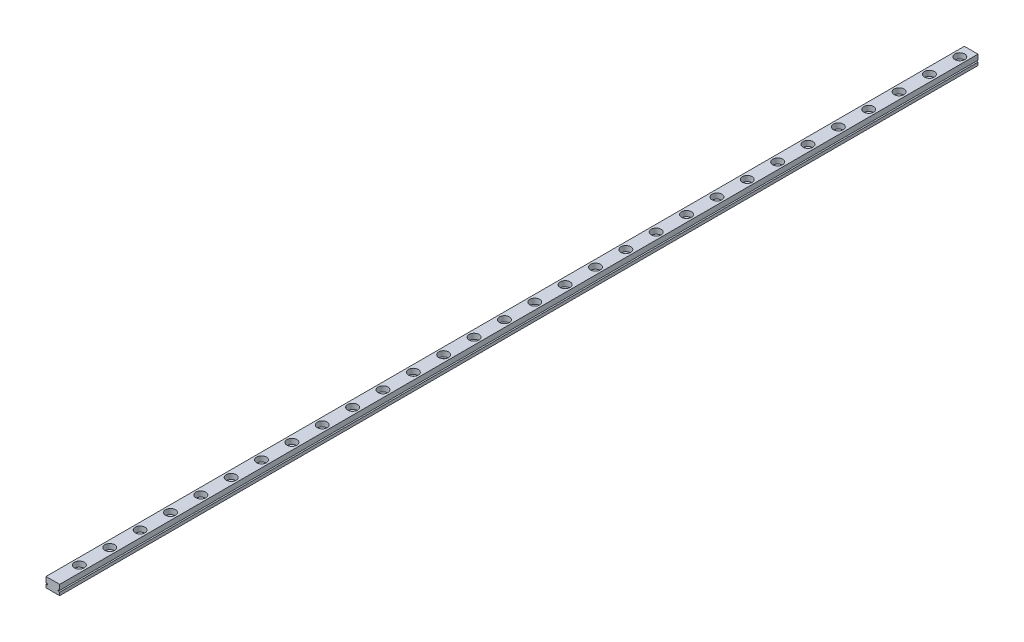
SolidWorks part; units mm, degrees
material "不锈钢 (铁素体)"
ref_plane "前视基准面" through (0, 0, 0) normal (0, 0, 1) x (1, 0, 0)
ref_plane "上视基准面" through (0, 0, 0) normal (0, 1, 0) x (1, 0, 0)
ref_plane "右视基准面" through (0, 0, 0) normal (1, 0, 0) x (0, 0, -1)
sketch "草图1" plane through (0, 0, 0) normal (0, 0, 1) x (1, 0, 0)
  line L1 (-4.5, 3.25) -> (4.5, 3.25)
  line L2 (-4.5, 3.25) -> (-4.5, -3.25)
  line L3 (-4.5, -3.25) -> (4.5, -3.25)
  line L4 (4.5, 3.25) -> (4.5, -3.25)
  line L5 (-4.5, 3.25) -> (4.5, -3.25) construction
  line L6 (-4.5, -3.25) -> (4.5, 3.25) construction
  point P0 (0, 0)
  dimension "D1" = 6.5
  dimension "D2" = 9
extrude "凸台-拉伸1" add sketch "草图1" along normal blind 608
sketch "草图2" plane through (0, 3.25, 0) normal (0, 1, 0) x (1, 0, 0)
  line L0 (0, 0) -> (0, -84.8716) construction
  line L1 (4.5, 0) -> (-4.5, 0) construction
  circle A0 centre (0, -7.5) radius 1.75
  circle A1 centre (0, -27.5) radius 1.75
  circle A2 centre (0, -47.5) radius 1.75
  circle A3 centre (0, -67.5) radius 1.75
  circle A4 centre (0, -87.5) radius 1.75
  circle A5 centre (0, -107.5) radius 1.75
  circle A6 centre (0, -127.5) radius 1.75
  circle A7 centre (0, -147.5) radius 1.75
  circle A8 centre (0, -167.5) radius 1.75
  circle A9 centre (0, -187.5) radius 1.75
  circle A10 centre (0, -207.5) radius 1.75
  circle A11 centre (0, -227.5) radius 1.75
  circle A12 centre (0, -247.5) radius 1.75
  circle A13 centre (0, -267.5) radius 1.75
  circle A14 centre (0, -287.5) radius 1.75
  circle A15 centre (0, -307.5) radius 1.75
  circle A16 centre (0, -327.5) radius 1.75
  circle A17 centre (0, -347.5) radius 1.75
  circle A18 centre (0, -367.5) radius 1.75
  circle A19 centre (0, -387.5) radius 1.75
  dimension "D1" = 3.5
  dimension "D2" = 7.5
  dimension "D4" = 20
  dimension "D3" = 20
extrude "切除-拉伸1" cut sketch "草图2" against normal through all
sketch "草图3" plane through (0, 3.25, 0) normal (0, 1, 0) x (1, 0, 0)
  circle A0 centre (0, -7.5) radius 3.25
  circle A1 centre (0, -27.5) radius 3.25
  circle A2 centre (0, -47.5) radius 3.25
  circle A3 centre (0, -67.5) radius 3.25
  circle A4 centre (0, -87.5) radius 3.25
  circle A5 centre (0, -107.5) radius 3.25
  circle A6 centre (0, -127.5) radius 3.25
  circle A7 centre (0, -147.5) radius 3.25
  circle A8 centre (0, -167.5) radius 3.25
  circle A9 centre (0, -187.5) radius 3.25
  circle A10 centre (0, -207.5) radius 3.25
  circle A11 centre (0, -227.5) radius 3.25
  circle A12 centre (0, -247.5) radius 3.25
  circle A13 centre (0, -267.5) radius 3.25
  circle A14 centre (0, -287.5) radius 3.25
  circle A15 centre (0, -307.5) radius 3.25
  circle A16 centre (0, -327.5) radius 3.25
  circle A17 centre (0, -347.5) radius 3.25
  circle A18 centre (0, -367.5) radius 3.25
  circle A19 centre (0, -387.5) radius 3.25
  dimension "D1" = 6.5
  dimension "D3" = 20
  dimension "D2" = 20
extrude "切除-拉伸2" cut sketch "草图3" against normal blind 3.5
sketch "草图4" plane through (0, 0, 0) normal (0, 0, -1) x (-1, 0, 0)
  line L0 (0, 3.25) -> (0, -3.25) construction
  line L1 (-4.5, 3.25) -> (4.5, 3.25) construction
  line L2 (4.5, -3.25) -> (-4.5, -3.25) construction
  line L3 (4.5, -0.25) -> (3.5, -0.45)
  line L4 (4.5, 3.25) -> (4.5, -3.25) construction
  line L5 (3.5, -0.45) -> (3.5, -1.05)
  line L6 (3.5, -1.05) -> (4.5, -1.25)
  line L7 (3.5, -0.75) -> (8.1318, -0.75) construction
  line L8 (4.5, -0.25) -> (4.5, -1.25)
  line L9 (-4.5, -0.25) -> (-3.5, -0.45)
  line L10 (-3.5, -0.45) -> (-3.5, -1.05)
  line L11 (-3.5, -1.05) -> (-4.5, -1.25)
  line L12 (-4.5, -0.25) -> (-4.5, -1.25)
  dimension "D1" = 1
  dimension "D2" = 1
  dimension "D3" = 0.6
  dimension "D4" = 4
extrude "切除-拉伸3" cut sketch "草图4" against normal through all
sketch "草图5" plane through (0, 3.25, 0) normal (0, 1, 0) x (1, 0, 0)
  line L0 (0, -387.5) -> (0, -407.5) construction
  circle A0 centre (0, -407.5) radius 3.25
  circle A1 centre (0, -427.5) radius 3.25
  circle A2 centre (0, -447.5) radius 3.25
  circle A3 centre (0, -467.5) radius 3.25
  circle A4 centre (0, -487.5) radius 3.25
  circle A5 centre (0, -507.5) radius 3.25
  circle A6 centre (0, -527.5) radius 3.25
  circle A7 centre (0, -547.5) radius 3.25
  circle A8 centre (0, -567.5) radius 3.25
  circle A9 centre (0, -587.5) radius 3.25
  dimension "D1" = 6.5
  dimension "D2" = 10
extrude "切除-拉伸4" cut sketch "草图5" against normal blind 3.5
sketch "草图6" plane through (0, -0.25, 0) normal (0, 1, 0) x (1, 0, 0)
  circle A0 centre (0, -407.5) radius 1.75
  circle A1 centre (0, -427.5) radius 1.75
  circle A2 centre (0, -447.5) radius 1.75
  circle A3 centre (0, -467.5) radius 1.75
  circle A4 centre (0, -487.5) radius 1.75
  circle A5 centre (0, -507.5) radius 1.75
  circle A6 centre (0, -527.5) radius 1.75
  circle A7 centre (0, -547.5) radius 1.75
  circle A8 centre (0, -567.5) radius 1.75
  circle A9 centre (0, -587.5) radius 1.75
  dimension "D1" = 3.5
  dimension "D2" = 10
extrude "切除-拉伸5" cut sketch "草图6" against normal through all
sketch "草图7" plane through (0, 3.25, 0) normal (0, 1, 0) x (1, 0, 0)
  line L0 (4.5, -608) -> (4.5, -605)
  line L1 (4.5, -608) -> (4.5, 0) construction
  line L2 (4.5, -605) -> (-4.5, -605)
  line L3 (-4.5, -608) -> (-4.5, 0) construction
  line L4 (-4.5, -605) -> (-4.5, -608)
  line L5 (-4.5, -608) -> (4.5, -608)
extrude "切除-拉伸6" cut sketch "草图7" against normal through all
